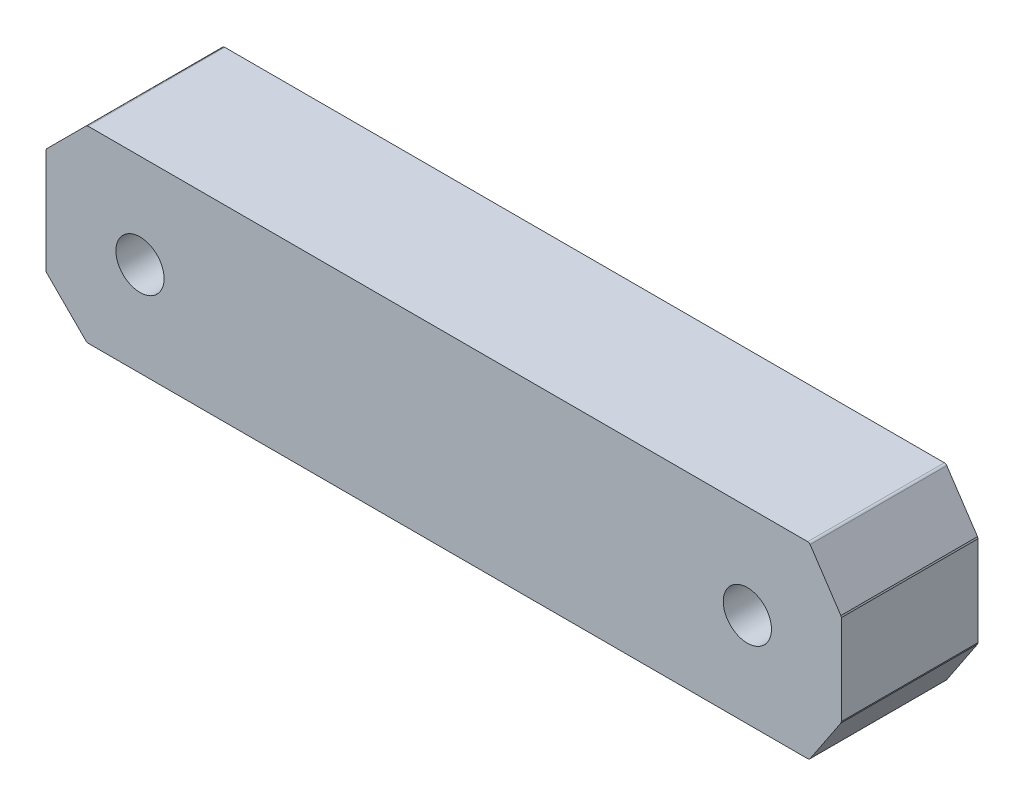
SolidWorks part; units mm, degrees
ref_plane "Front Plane" through (0, 0, 0) normal (0, 0, 1) x (1, 0, 0)
ref_plane "Top Plane" through (0, 0, 0) normal (0, 1, 0) x (1, 0, 0)
ref_plane "Right Plane" through (0, 0, 0) normal (1, 0, 0) x (0, 0, -1)
sketch "Sketch1" plane through (0, 0, 0) normal (0, 0, 1) x (1, 0, 0)
  line L0 (-24.7302, -6.4414) -> (-27.4414, -3.7302) construction
  line L1 (-24.7302, -6.4414) -> (-27.4414, -3.7302)
  line L2 (27.5, 3.111) -> (27.4664, 3.222)
  line L3 (-27.4414, 3.7302) -> (-24.7302, 6.4414) construction
  line L4 (27.4664, -3.222) -> (27.5, -3.111)
  line L6 (27.4664, -3.222) -> (25.3409, -6.4109) construction
  line L7 (27.5, 3.111) -> (27.5, -3.111) construction
  line L8 (25.3409, 6.4109) -> (27.4664, 3.222) construction
  line L10 (-27.5, -3.5887) -> (-27.5, 3.5887) construction
  line L11 (25.1745, 6.5) -> (-24.5887, 6.5)
  line L12 (-27.4414, 3.7302) -> (-24.7302, 6.4414)
  line L14 (-24.5887, -6.5) -> (25.1745, -6.5)
  line L15 (27.4664, -3.222) -> (25.3409, -6.4109)
  line L16 (27.5, 3.111) -> (27.5, -3.111)
  line L17 (25.3409, 6.4109) -> (27.4664, 3.222)
  line L19 (-27.5, -3.5887) -> (-27.5, 3.5887)
  arc A0 (-24.5887, 6.5) -> (-24.7302, 6.4414) centre (-24.5887, 6.3) ccw construction
  arc A1 (-27.4414, 3.7302) -> (-27.5, 3.5887) centre (-27.3, 3.5887) ccw construction
  arc A2 (-24.7302, -6.4414) -> (-24.5887, -6.5) centre (-24.5887, -6.3) ccw construction
  arc A3 (-27.5, -3.5887) -> (-27.4414, -3.7302) centre (-27.3, -3.5887) ccw construction
  arc A4 (25.1745, -6.5) -> (25.3409, -6.4109) centre (25.1745, -6.3) ccw construction
  arc A5 (25.3409, 6.4109) -> (25.1745, 6.5) centre (25.1745, 6.3) ccw construction
  circle A6 centre (21, 0) radius 1.666 construction
  circle A7 centre (-21, 0) radius 1.666 construction
  arc A8 (-24.5887, 6.5) -> (-24.7302, 6.4414) centre (-24.5887, 6.3) ccw
  arc A9 (-27.4414, 3.7302) -> (-27.5, 3.5887) centre (-27.3, 3.5887) ccw
  arc A10 (-24.7302, -6.4414) -> (-24.5887, -6.5) centre (-24.5887, -6.3) ccw
  arc A11 (-27.5, -3.5887) -> (-27.4414, -3.7302) centre (-27.3, -3.5887) ccw
  arc A12 (25.1745, -6.5) -> (25.3409, -6.4109) centre (25.1745, -6.3) ccw
  arc A13 (25.3409, 6.4109) -> (25.1745, 6.5) centre (25.1745, 6.3) ccw
  circle A14 centre (21, 0) radius 1.666
  circle A15 centre (-21, 0) radius 1.666
extrude "Boss-Extrude1" add sketch "Sketch1" along a picked direction on the side of the normal blind 9.45
